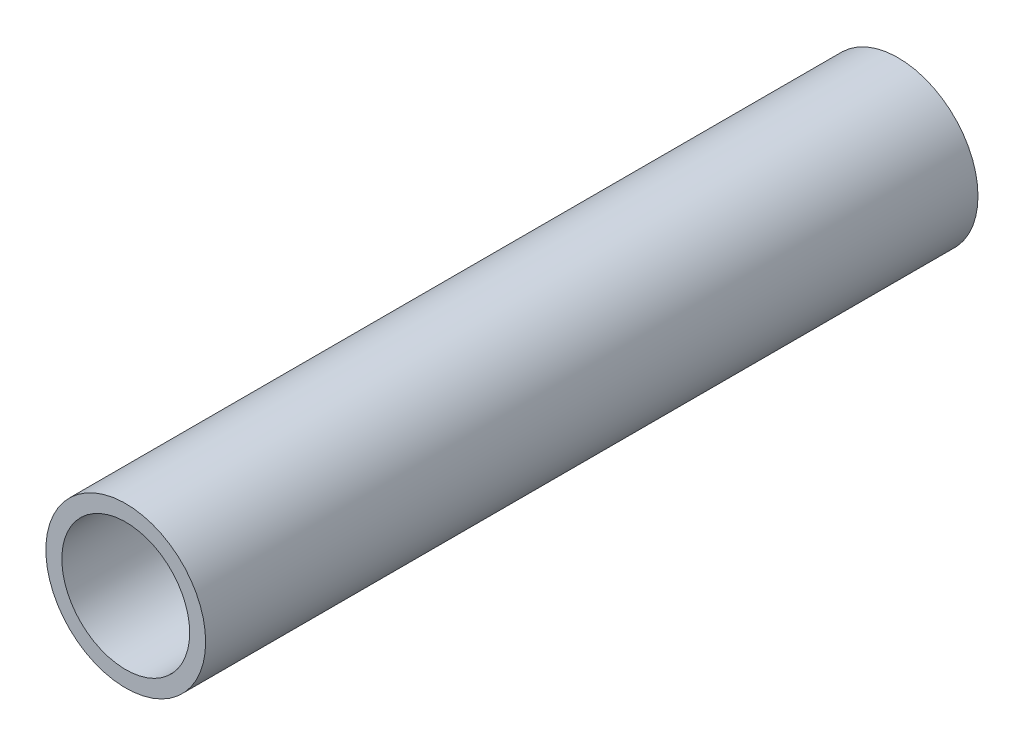
SolidWorks part; units mm, degrees
ref_plane "Front Plane" through (0, 0, 0) normal (0, 0, 1) x (1, 0, 0)
ref_plane "Top Plane" through (0, 0, 0) normal (0, 1, 0) x (1, 0, 0)
ref_plane "Right Plane" through (0, 0, 0) normal (1, 0, 0) x (0, 0, -1)
sketch "Sketch1" plane through (0, 0, 0) normal (0, 0, 1) x (1, 0, 0)
  circle A0 centre (0, 0) radius 19.05
  circle A1 centre (0, 0) radius 15.24
extrude "Boss-Extrude1" add sketch "Sketch1" along normal blind 184.15
